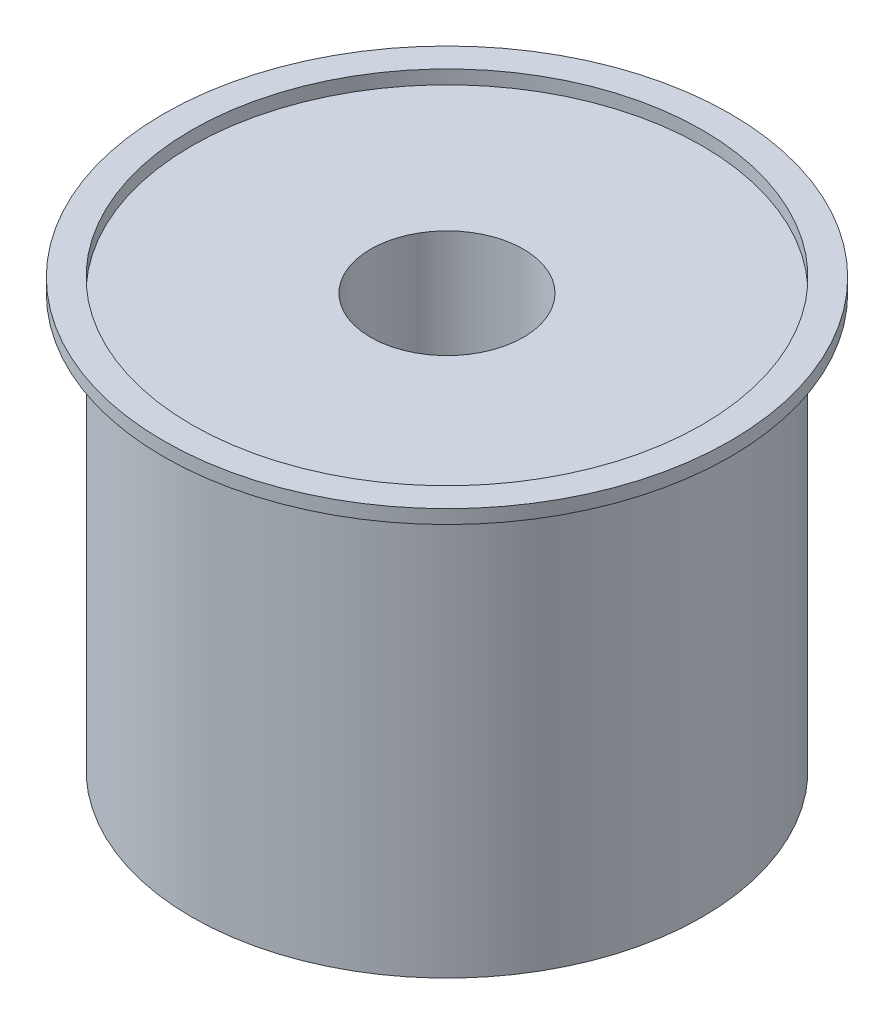
SolidWorks part; units mm, degrees
ref_plane "Alzado" through (0, 0, 0) normal (0, 0, 1) x (1, 0, 0)
ref_plane "Planta" through (0, 0, 0) normal (0, 1, 0) x (1, 0, 0)
ref_plane "Vista lateral" through (0, 0, 0) normal (1, 0, 0) x (0, 0, -1)
sketch "Croquis1" plane through (0, 0, 0) normal (0, 1, 0) x (1, 0, 0)
  circle A0 centre (0, 0) radius 55.5699
  circle A1 centre (0, 0) radius 185.5699
  dimension "D1" = 130
extrude "Saliente-Extruir1" add sketch "Croquis1" along normal blind 300
sketch "Croquis2" plane through (0, 300, 0) normal (0, 1, 0) x (1, 0, 0)
  circle A0 centre (0, 0) radius 205.9815
  circle A1 centre (0, 0) radius 185.5699
  circle A2 centre (0, 0) radius 185.5699
  circle A3 centre (0, 0) radius 185.5699 construction
  dimension "D2" = 411.9631
  dimension "D1" = 0
extrude "Saliente-Extruir2" add sketch "Croquis2" along normal blind 10 separate body
